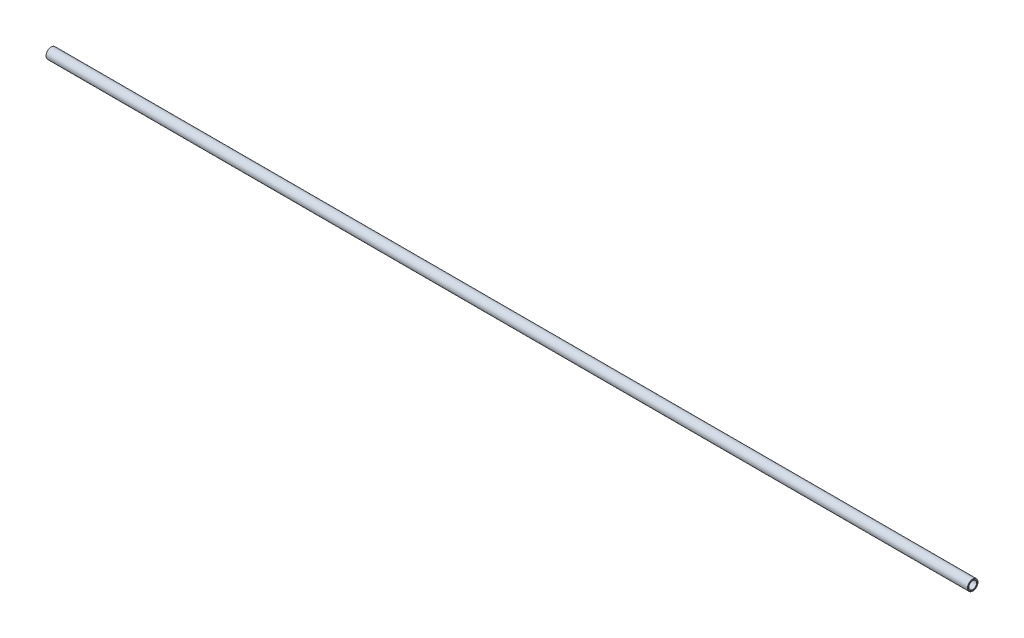
SolidWorks part; units mm, degrees
material "Carbon Fibre"
ref_plane "Front Plane" through (0, 0, 0) normal (0, 0, 1) x (1, 0, 0)
ref_plane "Top Plane" through (0, 0, 0) normal (0, 1, 0) x (1, 0, 0)
ref_plane "Right Plane" through (0, 0, 0) normal (1, 0, 0) x (0, 0, -1)
sketch "Sketch1" plane through (0, 0, 0) normal (1, 0, 0) x (0, 0, -1)
  circle A0 centre (0, 0) radius 12.7
  circle A1 centre (0, 0) radius 9.525
  dimension "D1" = 25.4
  dimension "D2" = 3.175
extrude "Boss-Extrude1" add sketch "Sketch1" along normal blind 2235.2
chamfer "Chamfer1" distance 0.508 angle 45 4 edges at (0, 0, -9.525) (0, 0, -12.7) (2235.2, 0, -12.7) (2235.2, 0, -9.525)
sketch "https://dragonplate.com/carbon-fiber-roll-wrapped-twill-tube-075-id-x-96-gloss-finish" [suppressed] plane through (0, 0, 0) normal (1, 0, 0) x (0, 0, -1)
  point P0 (0, 0)
